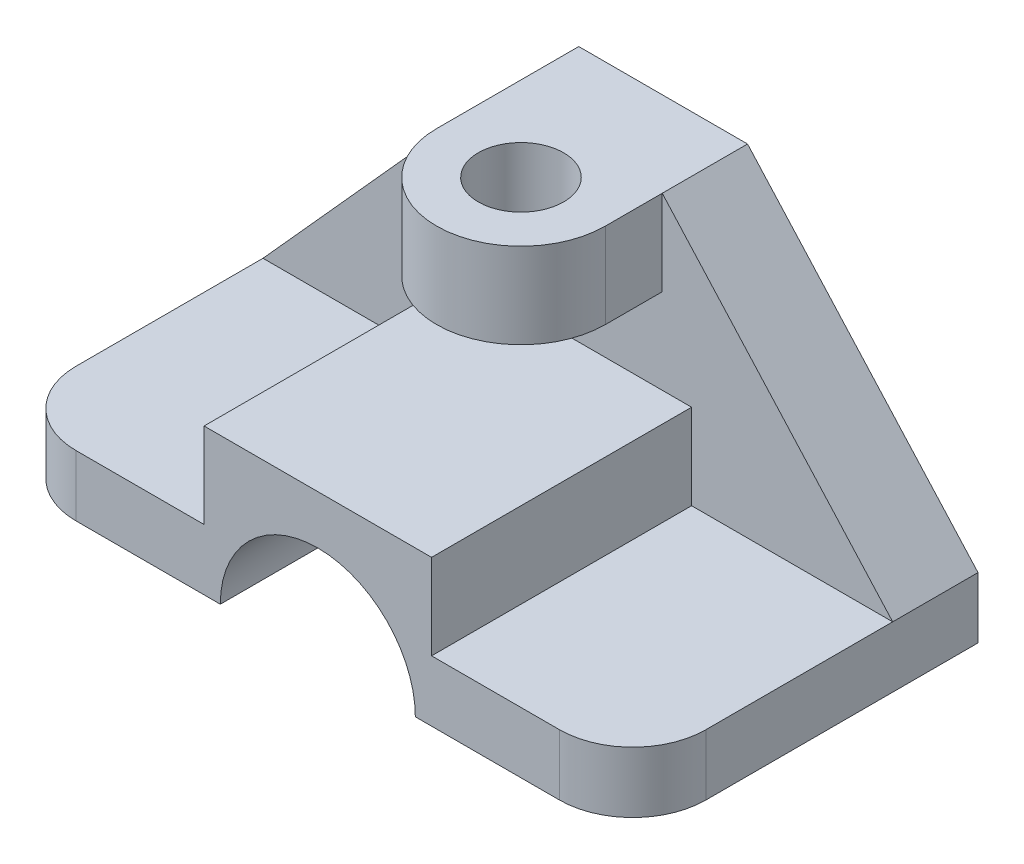
SolidWorks part; units mm, degrees
ref_plane "Front Plane" through (0, 0, 0) normal (0, 0, 1) x (1, 0, 0)
ref_plane "Top Plane" through (0, 0, 0) normal (0, 1, 0) x (1, 0, 0)
ref_plane "Right Plane" through (0, 0, 0) normal (1, 0, 0) x (0, 0, -1)
sketch "Sketch2" plane through (0, 0, 0) normal (0, 0, 1) x (1, 0, 0)
  line L1 (0, 0) -> (155, 0)
  line L2 (0, 0) -> (0, 78)
  line L3 (0, 78) -> (155, 78)
  line L4 (155, 0) -> (155, 78)
  dimension "D1" = 155
  dimension "D2" = 78
extrude "Boss-Extrude1" add sketch "Sketch2" along normal blind 21
sketch "Sketch3" plane through (0, 0, 21) normal (0, 0, 1) x (1, 0, 0)
  line L0 (0, 0) -> (155, 0) construction
  line L1 (0, 0) -> (53.5, 0)
  line L2 (155, 0) -> (101.5, 0)
  line L3 (0, 0) -> (0, 15)
  line L4 (0, 78) -> (0, 0) construction
  line L5 (49.5, 36) -> (105.5, 36)
  line L6 (77.5, 0) -> (77.5, 78) construction
  line L7 (155, 78) -> (0, 78) construction
  line L8 (0, 15) -> (49.5, 15)
  line L9 (49.5, 15) -> (49.5, 36)
  line L10 (155, 0) -> (155, 15)
  line L11 (155, 15) -> (105.5, 15)
  line L12 (105.5, 15) -> (105.5, 36)
  arc A0 (101.5, 0) -> (53.5, 0) centre (77.5, 0) ccw
  point P4 (77.5, 0)
  point P15 (77.5, 36)
  dimension "D1" = 24
  dimension "D2" = 15
  dimension "D3" = 56
  dimension "D4" = 36
extrude "Boss-Extrude2" add sketch "Sketch3" along normal blind 64
fillet "Fillet1" radius 18 2 edges at (155, 7.5, 85) (0, 7.5, 85)
sketch "Sketch4" plane through (0, 0, 21) normal (0, 0, 1) x (1, 0, 0)
  line L0 (0, 15) -> (56.7255, 78)
  line L1 (155, 78) -> (0, 78) construction
  line L2 (155, 15) -> (98.2745, 78)
  line L3 (49.5, 15) -> (0, 15) construction
  line L4 (155, 15) -> (105.5, 15) construction
  line L5 (0, 15) -> (0, 78)
  line L6 (0, 78) -> (56.7255, 78)
  line L7 (98.2745, 78) -> (155, 78)
  line L8 (155, 78) -> (155, 15)
  dimension "D1" = 48
  dimension "D2" = 48
extrude "Cut-Extrude1" cut sketch "Sketch4" against normal through all
sketch "Sketch5" plane through (0, 78, 0) normal (0, 1, 0) x (1, 0, 0)
  line L0 (77.5, 0) -> (77.5, -35) construction
  line L1 (98.2745, 0) -> (56.7255, 0) construction
  line L2 (56.7255, 0) -> (56.7255, -35)
  line L3 (56.7255, 0) -> (98.2745, 0)
  line L4 (98.2745, 0) -> (98.2745, -35)
  circle A0 centre (77.5, -35) radius 10.5
  arc A1 (56.7255, -35) -> (98.2745, -35) centre (77.5, -35) ccw
  dimension "D2" = 21
  dimension "D1" = 35
extrude "Boss-Extrude3" add sketch "Sketch5" against normal blind 21
